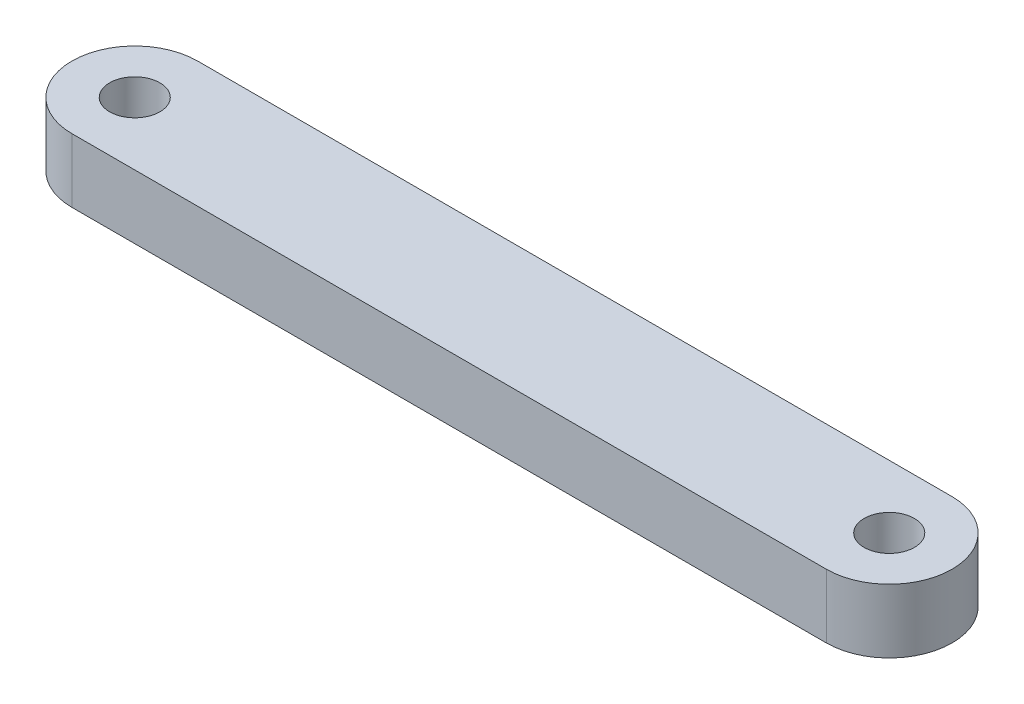
SolidWorks part; units mm, degrees
ref_plane "Front Plane" through (0, 0, 0) normal (0, 0, 1) x (1, 0, 0)
ref_plane "Top Plane" through (0, 0, 0) normal (0, 1, 0) x (1, 0, 0)
ref_plane "Right Plane" through (0, 0, 0) normal (1, 0, 0) x (0, 0, -1)
sketch "Sketch1" plane through (0, 0, 0) normal (0, 1, 0) x (1, 0, 0)
  line L1 (-15, 2.5) -> (15, 2.5)
  line L3 (-15, -2.5) -> (15, -2.5)
  line L5 (-15, 2.5) -> (15, -2.5) construction
  line L6 (-15, -2.5) -> (15, 2.5) construction
  arc A0 (-15, 2.5) -> (-15, -2.5) centre (-15, 0) ccw
  arc A1 (15, 2.5) -> (15, -2.5) centre (15, 0) cw
  point P0 (0, 0)
  dimension "D1" = 30
  dimension "D2" = 5
extrude "Boss-Extrude1" add sketch "Sketch1" along normal blind 2.54
sketch "Sketch2" plane through (0, 0, 0) normal (0, 1, 0) x (1, 0, 0)
  line L0 (0, 0) -> (0, 5.9817) construction
  circle A0 centre (-15, 0) radius 1
  circle A1 centre (15, 0) radius 1
  dimension "D1" = 2
  dimension "D2" = 30
extrude "Cut-Extrude1" cut sketch "Sketch2" against normal through all both and the other way through all
